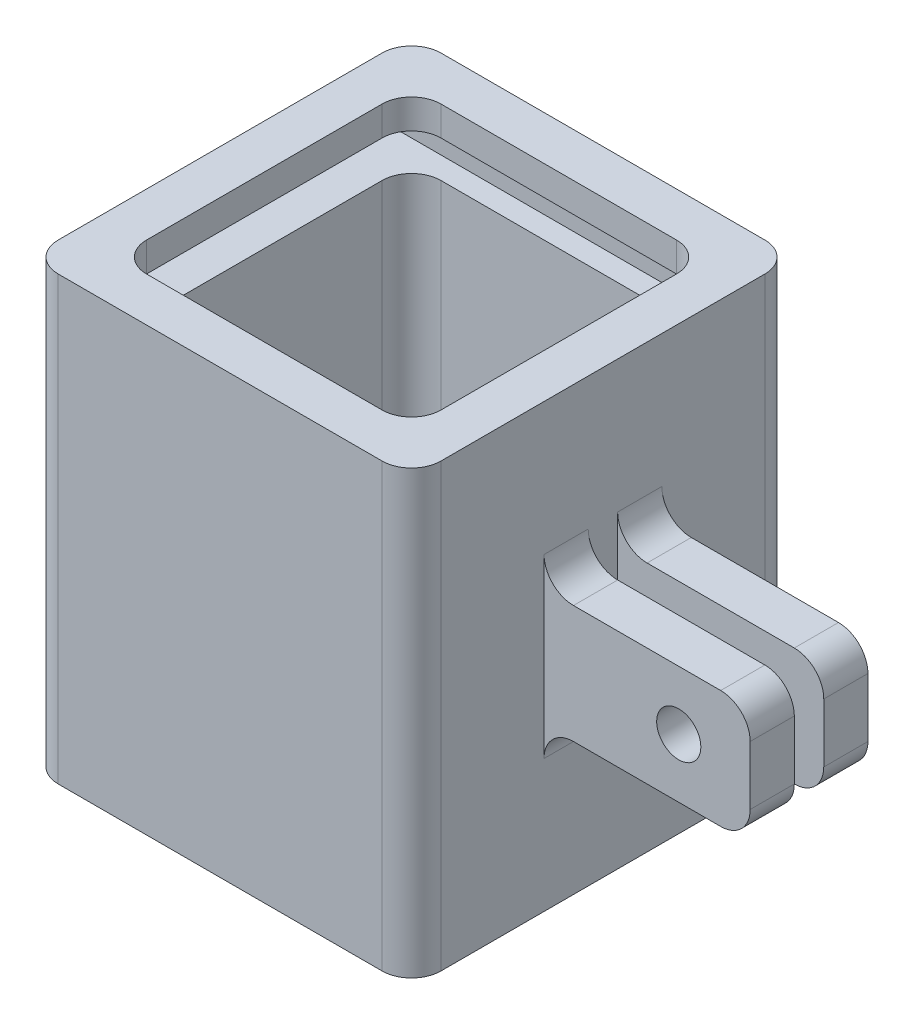
SolidWorks part; units mm, degrees
material "ABS"
ref_plane "Front Plane" through (0, 0, 0) normal (0, 0, 1) x (1, 0, 0)
ref_plane "Top Plane" through (0, 0, 0) normal (0, 1, 0) x (1, 0, 0)
ref_plane "Right Plane" through (0, 0, 0) normal (1, 0, 0) x (0, 0, -1)
sketch "Sketch1" plane through (0, 0, 0) normal (0, 1, 0) x (1, 0, 0)
  line L1 (-13, 13) -> (13, 13)
  line L2 (-13, 13) -> (-13, -13)
  line L3 (-13, -13) -> (13, -13)
  line L4 (13, 13) -> (13, -13)
  line L5 (-10, 10) -> (10, 10)
  line L6 (-10, 10) -> (-10, -10)
  line L7 (-10, -10) -> (10, -10)
  line L8 (10, 10) -> (10, -10)
  dimension "D1" = 20
  dimension "D2" = 20
  dimension "D3" = 10
  dimension "D4" = 10
  dimension "D5" = 26
  dimension "D6" = 26
  dimension "D7" = 13
  dimension "D8" = 13
extrude "Boss-Extrude1" add sketch "Sketch1" along normal blind 30
sketch "Sketch2" plane through (0, 0, 0) normal (0, -1, 0) x (1, 0, 0)
  line L1 (-10, 10) -> (10, 10)
  line L2 (-10, 10) -> (-10, -10)
  line L3 (-10, -10) -> (10, -10)
  line L4 (10, 10) -> (10, -10)
extrude "Boss-Extrude2" add sketch "Sketch2" against normal blind 5
fillet "Fillet1" radius 2 8 edges at (-10, 17.5, -10) (10, 17.5, -10) (10, 17.5, 10) (-10, 17.5, 10) (-13, 15, 13) (-13, 15, -13) (13, 15, -13) (13, 15, 13)
sketch "Sketch6" plane through (13, 0, 0) normal (1, 0, 0) x (0, 0, -1)
  line L0 (-11, 0) -> (11, 0) construction
  line L1 (-4, 19) -> (-1, 19)
  line L2 (-4, 19) -> (-4, 11)
  line L3 (-4, 11) -> (-1, 11)
  line L4 (-1, 19) -> (-1, 11)
  line L5 (0, 0) -> (0, 30) construction
  line L6 (-11, 30) -> (11, 30) construction
  line L7 (1, 19) -> (1, 11)
  line L8 (4, 11) -> (1, 11)
  line L9 (4, 19) -> (4, 11)
  line L10 (4, 19) -> (1, 19)
  dimension "D1" = 3
  dimension "D2" = 8
  dimension "D3" = 11
  dimension "D4" = 1
extrude "Boss-Extrude4" add sketch "Sketch6" along normal blind 14
fillet "Fillet2" radius 2 4 edges at (13, 11, -2.5) (13, 11, 2.5) (13, 19, 2.5) (13, 19, -2.5)
fillet "Fillet3" radius 2 4 edges at (27, 11, -2.5) (27, 11, 2.5) (27, 19, -2.5) (27, 19, 2.5)
sketch "Sketch7" plane through (0, 0, -4) normal (0, 0, -1) x (-1, 0, 0)
  line L0 (-13, 0) -> (-13, 30) construction
  line L1 (-25, 19) -> (-15, 19) construction
  circle A0 centre (-22.15, 15) radius 1.5
  dimension "D1" = 3
  dimension "D2" = 9.15
  dimension "D3" = 4
extrude "Cut-Extrude2" cut sketch "Sketch7" against normal through all both and the other way through all
sketch "Sketch9" plane through (-13, 0, 0) normal (-1, 0, 0) x (0, 0, 1)
  line L0 (-11, 30) -> (-11, 0) construction
  line L1 (-11.5, 28) -> (11.5, 28)
  line L2 (-11.5, 28) -> (-11.5, 25.5)
  line L3 (-11.5, 25.5) -> (11.5, 25.5)
  line L4 (11.5, 28) -> (11.5, 25.5)
  line L5 (11, 0) -> (11, 30) construction
  line L6 (-11, 30) -> (11, 30) construction
  dimension "D1" = 0.5
  dimension "D2" = 0.5
  dimension "D3" = 2
  dimension "D4" = 2.5
extrude "Cut-Extrude3" cut sketch "Sketch9" against normal up to surface (23 mm away) up to face at (10, 17.5, 0)
fillet "Fillet4" radius 2 2 edges at (10, 26.75, 11.5) (10, 26.75, -11.5)
